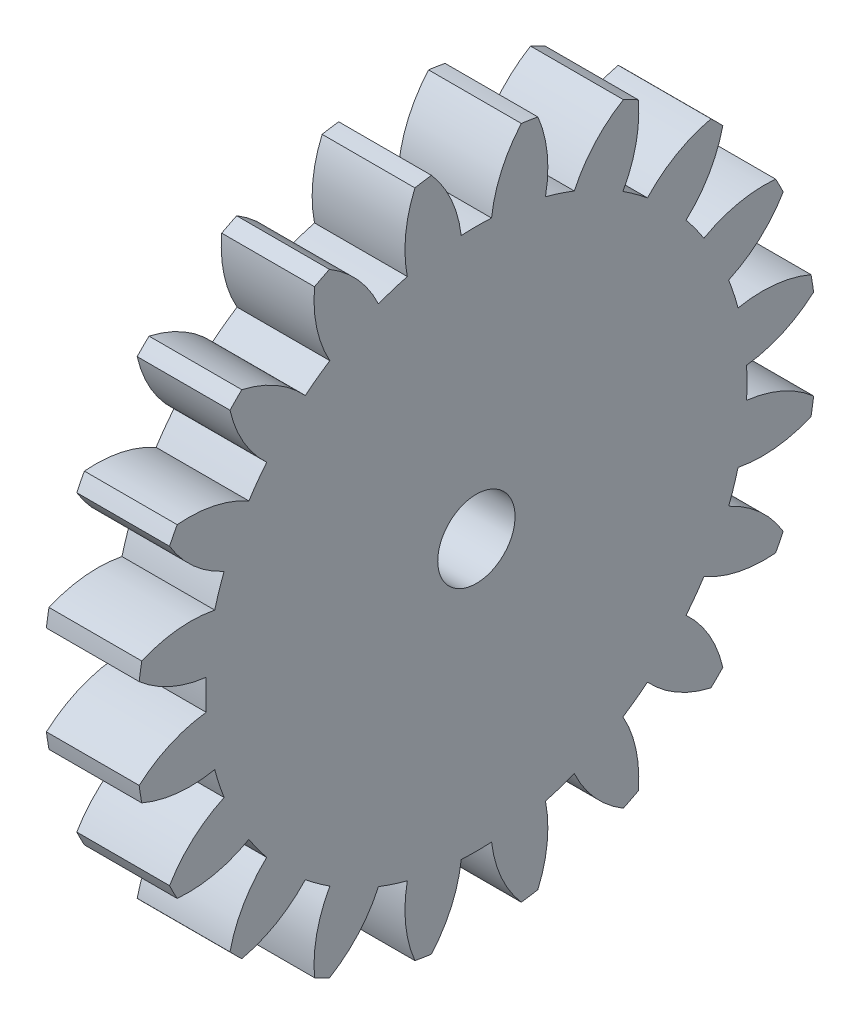
SolidWorks part; units mm, degrees
ref_plane "Plane1" through (0, 0, 0) normal (0, 0, 1) x (1, 0, 0)
ref_plane "Plane2" through (0, 0, 0) normal (0, 1, 0) x (1, 0, 0)
ref_plane "Plane3" through (0, 0, 0) normal (1, 0, 0) x (0, 0, -1)
sketch "HoldingSke" plane through (0, 0, 0) normal (0, 1, 0) x (1, 0, 0)
  line L0 (0, 0) -> (0.2349, -0.0855)
  line L1 (-15, 0) -> (100, 0) construction
  line L2 (0, 0) -> (-2.1039, 2.3779)
  line L3 (0, 0) -> (-11.863, 4.5341)
  line L4 (0, 0) -> (8.1152, 2.9537)
  line L5 (0, 0) -> (-46.8476, -17.4728)
  line L6 (0, 0) -> (-9.9476, -6.7116)
  line L7 (-2.1039, 2.3779) -> (8.6586, 51.2059)
  line L8 (-76.2, 54.61) -> (-74.4, 54.61)
  line L9 (-71.009, 38.7566) -> (-53.1078, 45.2721)
  line L10 (-76.2, 71.12) -> (104.1128, 71.12)
  line L11 (0, 0) -> (-12, 0)
  line L12 (-76.2, 101.6) -> (-76.073, 101.6)
  line L13 (24.9733, 27.94) -> (52.9518, 28.4284)
  line L14 (24.9733, 27.94) -> (24.9743, 27.94)
  line L15 (24.9733, 27.94) -> (100.4006, 29.5858)
  line L16 (-63.627, -4) -> (-12.827, -4)
  circle A0 centre (0, 0) radius 5
  circle A1 centre (0, 0) radius 34.999
  circle A2 centre (0, 0) radius 37.5
  circle A3 centre (0, 0) radius 5
  dimension "MHD" = 69.998
  dimension "Hub_dia" = 75
  dimension "Bore" = 10
  dimension "MBD" = 10
  dimension "Num_teeth" = 20
  dimension "Pitch" = 0.25
  dimension "Overall_len" = 50
  dimension "Show_teeth" = 20
  dimension "Thickness" = 12
  dimension "OAL" = 50.0001
  dimension "T_dim" = 1.8
  dimension "Ap" = 20
  dimension "H" = 19.05
  dimension "Pitch_radius" = 180.3128
  dimension "Width" = 12
  dimension "Backlash" = 0.127
  dimension "Addendum_fac" = 1
  dimension "Dedendum_fac" = 1.25
  dimension "Clearance_fac" = 0.25
  dimension "Dedendum_add" = 0.001
  dimension "Module" = 4
sketch "BasProSke" plane through (0, 0, 0) normal (0, 1, 0) x (1, 0, 0)
  line L0 (-10, 0) -> (60, 0) construction
  line L1 (0, 0) -> (0, 44)
  line L2 (0, 0) -> (12, 0)
  line L3 (12, 0) -> (12, 44)
  line L4 (12, 44) -> (0, 44)
  dimension "Thickness" = 12
  dimension "Diameter" = 88
revolve "Base-Revolve" add sketch "BasProSke" angle 360 about L0
sketch "TooCutSke" plane through (0, 0, 0) normal (1, 0, 0) x (0, 0, -1)
  line L1 (0, 0) -> (0, 107) construction
  line L2 (0, 0) -> (-3.3605, 39.8586) construction
  line L3 (0, 0) -> (-12.4815, 78.8048) construction
  line L4 (-3.3605, 39.8586) -> (-6.2407, 39.4024) construction
  arc A0 (1.9617, 34.944) -> (-1.9617, 34.944) centre (0, 0) ccw
  arc A1 (5.8321, 43.6374) -> (-5.8321, 43.6374) centre (0, 0) ccw
  circle A2 centre (0, 0) radius 40 construction
  circle A3 centre (0, 0) radius 37.5877 construction
  arc A4 (-1.9617, 34.944) -> (-5.8321, 43.6374) centre (-17.8525, 33.0775) ccw
  arc A5 (5.8321, 43.6374) -> (1.9617, 34.944) centre (17.8525, 33.0775) ccw
  dimension "Root_dia" = 69.998
  dimension "Overcut_dia" = 88.0508
  dimension "Pitch_dia" = 80
  dimension "Base_dia" = 75.1754
  dimension "Flank_rad" = 16
  dimension "Half_ang" = 9
  dimension "Half_CT" = 2.9161
extrude "ToothCut" cut sketch "TooCutSke" along normal through all
fillet "Breaks" [suppressed] radius 0.08
fillet "RootFillets" [suppressed] radius 1.001
pattern_circular "TeethCuts" count 20 every 18 about axis through (-10, 0, 0) along (1, 0, 0) of "ToothCut", "RootFillets", "Breaks"
sketch "HubNeaOneSke" plane through (0, 0, 0) normal (-1, 0, 0) x (0, 0, 1)
  circle A0 centre (0, 0) radius 34.999
  dimension "Diameter" = 69.998
extrude "HubNearOne" [suppressed] add sketch "HubNeaOneSke" along normal blind 38.0001
sketch "HubNeaBotSke" plane through (0, 0, 0) normal (-1, 0, 0) x (0, 0, 1)
  circle A0 centre (0, 0) radius 34.999
  dimension "Diameter" = 69.998
extrude "HubNearBoth" [suppressed] add sketch "HubNeaBotSke" along normal blind 19
ref_plane "FarPln" through (12, 0, 0) normal (1, 0, 0) x (0, 0, -1)
sketch "HubFarSke" plane through (12, 0, 0) normal (1, 0, 0) x (0, 0, -1)
  circle A0 centre (0, 0) radius 34.999
  dimension "Diameter" = 69.998
extrude "HubFar" [suppressed] add sketch "HubFarSke" along normal blind 19
sketch "BorSke" plane through (0, 0, 0) normal (1, 0, 0) x (0, 0, -1)
  circle A0 centre (0, 0) radius 5
  dimension "Diameter" = 10
extrude "Bore" cut sketch "BorSke" along normal mid plane 100.0001
sketch "KeySke" plane through (0, 0, 0) normal (1, 0, 0) x (0, 0, -1)
  line L0 (-2, 0) -> (-2, 6.8)
  line L1 (-2, 6.8) -> (2, 6.8)
  line L2 (2, 6.8) -> (2, 0)
  line L3 (0, 0) -> (0, 34) construction
  line L4 (-2, 0) -> (2, 0)
  dimension "Offset" = 6.8
  dimension "Width" = 4
extrude "Keyway" [suppressed] cut sketch "KeySke" along normal mid plane 100.0001
pattern_circular "Keyway2" [suppressed] count 2 every 90 about axis through (-10, 0, 0) along (1, 0, 0)
equation "' \"Module@HoldingSke\" = 6.35"
equation "' \"Num_teeth@HoldingSke\" = 12"
equation "' \"Ap@HoldingSke\" =  20"
equation "' \"Ap@HoldingSke\" = 20"
equation "' \"Width@HoldingSke\" = 0.5 * 25.4"
equation "' \"Hub_dia@HoldingSke\"= 1 * 25.4"
equation "' \"Hub_dia@HoldingSke\" = 1 * 25.4"
equation "' \"Overall_len@HoldingSke\" = 1.0 * 25.4"
equation "' \"Bore@HoldingSke\" = 0.75 * 25.4"
equation "' \"T_dim@HoldingSke\" = 0.1 * 25.4"
equation "' \"Width@KeySke\" = 0.25 * 25.4"
equation "' \"Show_teeth@HoldingSke\" = 13"
equation "' \"Backlash@HoldingSke\" = 0.009 * 25.4"
equation "' \"Addendum_fac@HoldingSke\" = 1.0"
equation "' \"Dedendum_fac@HoldingSke\" = 1.25"
equation "' \"Dedendum_add@HoldingSke\" = 0.00005 * 25.4"
equation "' \"Clearance_fac@HoldingSke\" = 0.25"
equation "\"Pitch@HoldingSke\" = 1 / \"Module@HoldingSke\""
equation "\"Overcut_dia@TooCutSke\" = (\"Num_teeth@HoldingSke\" + 2 * \"Addendum_fac@HoldingSke\") / \"Pitch@HoldingSke\" + 0.002 * 25.4"
equation "\"Pitch_dia@TooCutSke\" = \"Num_teeth@HoldingSke\" / \"Pitch@HoldingSke\""
equation "\"Base_dia@TooCutSke\" = \"Num_teeth@HoldingSke\" / \"Pitch@HoldingSke\" * cos((\"Ap@HoldingSke\"  * 3.14159265 / 180))"
equation "\"Root_dia@TooCutSke\" = (\"Num_teeth@HoldingSke\" + 2) / \"Pitch@HoldingSke\" - 2 * (\"Addendum_fac@HoldingSke\" + \"Dedendum_fac@HoldingSke\") / \"Pitch@HoldingSke\" - \"Dedendum_add@HoldingSke\" * 2"
equation "\"Half_ang@TooCutSke\" = 180 / \"Num_teeth@HoldingSke\""
equation "\"Half_CT@TooCutSke\" = \"Num_teeth@HoldingSke\" / \"Pitch@HoldingSke\" * sin((3.14159265 / 2 / \"Num_teeth@HoldingSke\")) / 2 - 7 * \"Backlash@HoldingSke\" / 4"
equation "\"Flank_rad@TooCutSke\" = \"Num_teeth@HoldingSke\" / \"Pitch@HoldingSke\" / 5"
equation "\"Radius@RootFillets\" = \"Clearance_fac@HoldingSke\" / \"Pitch@HoldingSke\" + \"Dedendum_add@HoldingSke\""
equation "\"Break_rad@Breaks\" = 0.02 / \"Pitch@HoldingSke\""
equation "\"Thickness@HoldingSke\" = \"Width@HoldingSke\""
equation "\"OAL@HoldingSke\" = \"Thickness@HoldingSke\""
equation "\"MHD@HoldingSke\" = (\"Num_teeth@HoldingSke\" + 2) / \"Pitch@HoldingSke\" - 2 * (\"Addendum_fac@HoldingSke\" + \"Dedendum_fac@HoldingSke\")  / \"Pitch@HoldingSke\" - \"Dedendum_add@HoldingSke\" * 2"
equation "\"MBD@HoldingSke\" = (\"Num_teeth@HoldingSke\" + 2) / \"Pitch@HoldingSke\" - 2 * (\"Addendum_fac@HoldingSke\" + \"Dedendum_fac@HoldingSke\")  / \"Pitch@HoldingSke\" - \"Dedendum_add@HoldingSke\" * 2 - 0.002 * 25.4"
equation "\"MHD@HoldingSke\" = ((sgn( \"MHD@HoldingSke\" - \"Hub_dia@HoldingSke\" )-1)*( \"MHD@HoldingSke\" - \"Hub_dia@HoldingSke\" ))/-2+ \"Hub_dia@HoldingSke\""
equation "\"MBD@HoldingSke\" = ((sgn( \"MBD@HoldingSke\" - \"Bore@HoldingSke\" )-1)*( \"MBD@HoldingSke\" - \"Bore@HoldingSke\" ))/-2+ \"Bore@HoldingSke\""
equation "\"OAL@HoldingSke\" = ((sgn( \"OAL@HoldingSke\" - \"Overall_len@HoldingSke\" )+1)*( \"OAL@HoldingSke\" - \"Overall_len@HoldingSke\" ))/2 + \"Overall_len@HoldingSke\" + 0.000002 * 25.4"
equation "\"Num_teeth@TeethCuts\" = int( \"Show_teeth@HoldingSke\" ) + 1"
equation "\"Num_teeth@TeethCuts\" = ((sgn( \"Num_teeth@TeethCuts\" - \"Num_teeth@HoldingSke\" )-1)*( \"Num_teeth@TeethCuts\" - \"Num_teeth@HoldingSke\" ))/-2+ \"Num_teeth@HoldingSke\""
equation "\"Num_teeth@TeethCuts\" = ((sgn( \"Num_teeth@TeethCuts\" - 2.0)+1)*( \"Num_teeth@TeethCuts\" - 2.0))/2 +2.0"
equation "\"Angle@TeethCuts\" = 360.0 / \"Num_teeth@HoldingSke\""
equation "\"Diameter@BasProSke\" = (\"Num_teeth@HoldingSke\" + 2 * \"Addendum_fac@HoldingSke\") / \"Pitch@HoldingSke\""
equation "\"Thickness@BasProSke\"  = \"Thickness@HoldingSke\""
equation "' \"Fillet_rad@BasProSke\" =  \"Thickness@HoldingSke\" * 0.05"
equation "' \"Fillet_rad@BasProSke\" = \"Thickness@HoldingSke\" * 0.05"
equation "\"MHD@HoldingSke\" = ((sgn( \"MHD@HoldingSke\" - \"Root_dia@TooCutSke\" )-1)*( \"MHD@HoldingSke\" - \"Root_dia@TooCutSke\" ))/-2+ \"Root_dia@TooCutSke\""
equation "\"Diameter@HubNeaOneSke\" = \"MHD@HoldingSke\""
equation "\"Length@HubNearOne\" = \"OAL@HoldingSke\" - \"Thickness@BasProSke\""
equation "\"Diameter@HubNeaBotSke\" = \"MHD@HoldingSke\""
equation "\"Length@HubNearBoth\" = ( \"OAL@HoldingSke\" - \"Thickness@BasProSke\" ) / 2.0"
equation "\"Thickness@FarPln\" = \"Thickness@BasProSke\""
equation "\"Diameter@HubFarSke\" = \"MHD@HoldingSke\""
equation "\"Length@HubFar\" = ( \"OAL@HoldingSke\" - \"Thickness@BasProSke\" ) / 2.0"
equation "\"Diameter@BorSke\" = \"MBD@HoldingSke\""
equation "\"D1@Bore\" = \"OAL@HoldingSke\" * 2.0"
equation "\"D1@Keyway\" = \"OAL@HoldingSke\" * 2.0"
equation "\"Offset@KeySke\" = \"T_dim@HoldingSke\" + \"MBD@HoldingSke\" / 2.0"
